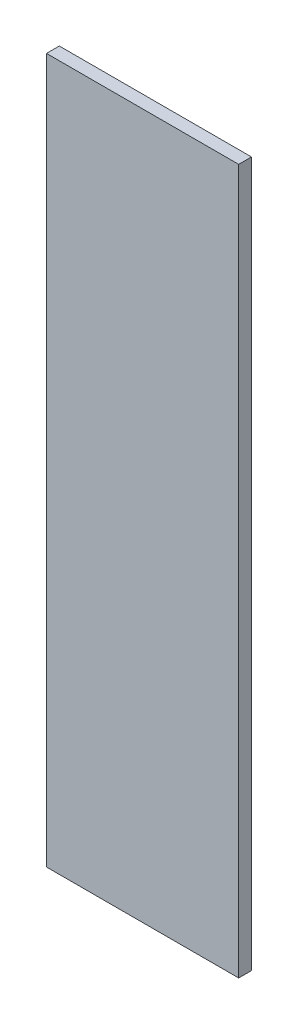
SolidWorks part; units mm, degrees
ref_plane "Ebene vorne" through (0, 0, 0) normal (0, 0, 1) x (1, 0, 0)
ref_plane "Ebene oben" through (0, 0, 0) normal (0, 1, 0) x (1, 0, 0)
ref_plane "Ebene rechts" through (0, 0, 0) normal (1, 0, 0) x (0, 0, -1)
sketch "Skizze1" plane through (0, 0, 0) normal (0, 0, 1) x (1, 0, 0)
  line L1 (-11.2355, 17.4324) -> (18.7645, 17.4324)
  line L2 (-11.2355, 17.4324) -> (-11.2355, -92.5676)
  line L3 (-11.2355, -92.5676) -> (18.7645, -92.5676)
  line L4 (18.7645, 17.4324) -> (18.7645, -92.5676)
  dimension "D1" = 30
  dimension "D2" = 110
extrude "Aufsatz-Linear austragen1" add sketch "Skizze1" along normal blind 2
